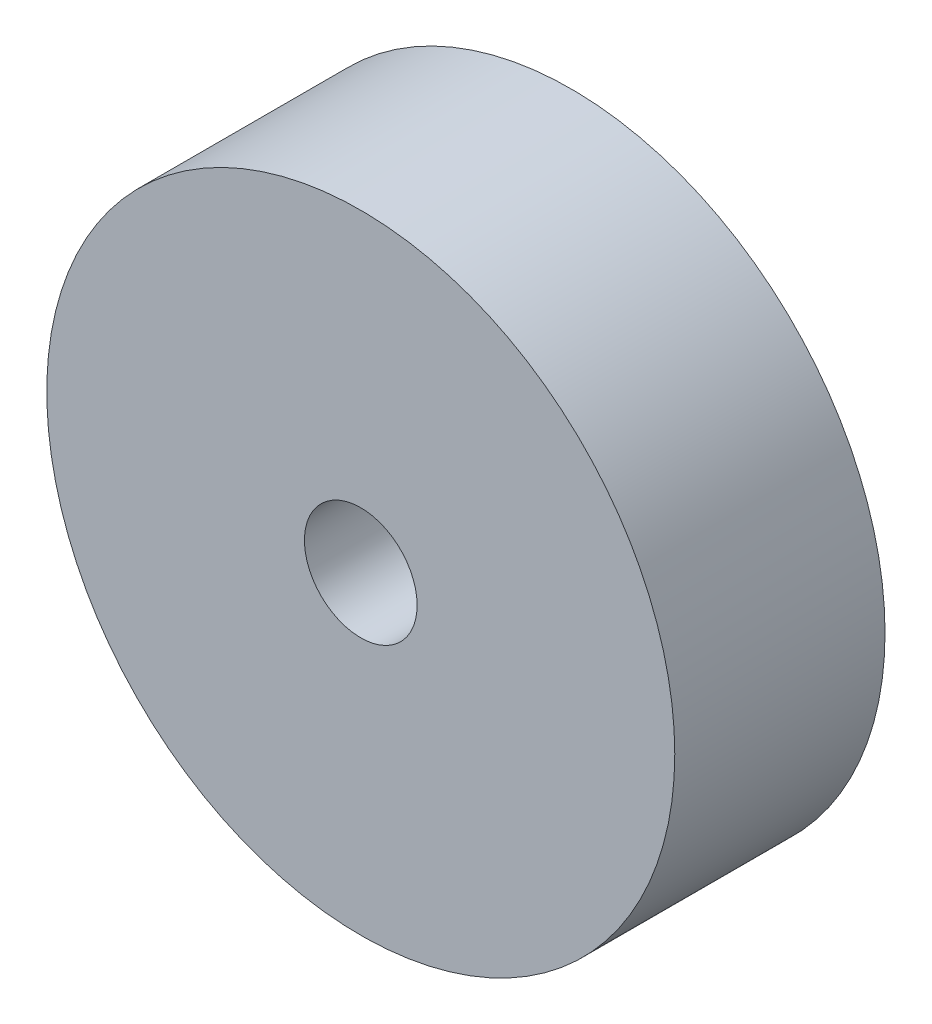
SolidWorks part; units mm, degrees
material "Delrin 2700 NC010, Low Viscosity Acetal Copolymer (SS)"
ref_plane "Front Plane" through (0, 0, 0) normal (0, 0, 1) x (1, 0, 0)
ref_plane "Top Plane" through (0, 0, 0) normal (0, 1, 0) x (1, 0, 0)
ref_plane "Right Plane" through (0, 0, 0) normal (1, 0, 0) x (0, 0, -1)
sketch "Sketch1" plane through (0, 0, 0) normal (0, 0, 1) x (1, 0, 0)
  circle A0 centre (0, 0) radius 14.224
  dimension "D1" = 28.448
extrude "Boss-Extrude1" add sketch "Sketch1" along normal blind 9.525
hole_wizard "#10 Clearance Hole1" positions "Sketch2" profile "Sketch3" hole size "#10" standard "ANSI Inch" end condition through all
sketch "Sketch2" plane through (0, 0, 9.525) normal (0, 0, 1) x (1, 0, 0)
  point P0 (0, 0)
sketch "Sketch3" plane through (0, 0, 9.525) normal (1, 0, 0) x (0, -1, 0)
  line L0 (0, 0) -> (0, 9.525)
  line L1 (0, 9.525) -> (2.5527, 9.525)
  line L2 (2.5527, 9.525) -> (2.5527, 0)
  line L5 (2.5527, 0) -> (0, 0)
  line L11 (0, -6.35) -> (0, 107.95) construction
  dimension "Thru Hole Dia." = 5.1054
  dimension "Thru Hole Depth" = 9.525
